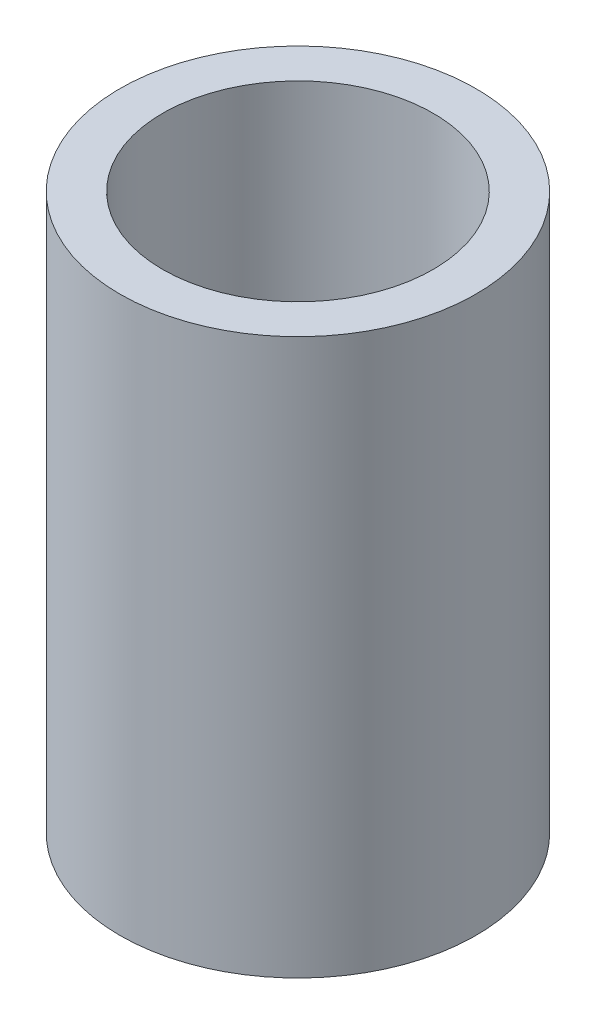
SolidWorks part; units mm, degrees
material "Caucho"
ref_plane "Alzado" through (0, 0, 0) normal (0, 0, 1) x (1, 0, 0)
ref_plane "Planta" through (0, 0, 0) normal (0, 1, 0) x (1, 0, 0)
ref_plane "Vista lateral" through (0, 0, 0) normal (1, 0, 0) x (0, 0, -1)
sketch "Croquis1" plane through (0, 0, 0) normal (0, 1, 0) x (1, 0, 0)
  circle A0 centre (0, 0) radius 9.5
  circle A1 centre (0, 0) radius 12.5
  dimension "D1" = 3
  dimension "D2" = 19
extrude "Saliente-Extruir1" add sketch "Croquis1" along normal blind 39
